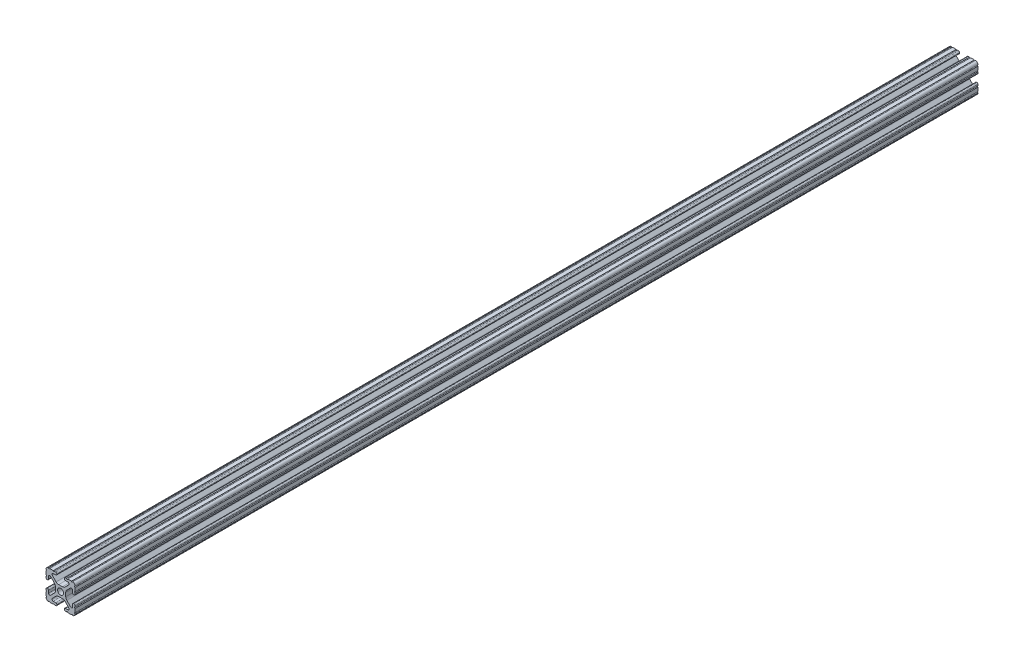
SolidWorks part; units mm, degrees
ref_plane "Front Plane" through (0, 0, 0) normal (0, 0, 1) x (1, 0, 0)
ref_plane "Top Plane" through (0, 0, 0) normal (0, 1, 0) x (1, 0, 0)
ref_plane "Right Plane" through (0, 0, 0) normal (1, 0, 0) x (0, 0, -1)
sketch "Sketch1" plane through (0, 0, 0) normal (0, 0, 1) x (1, 0, 0)
  line L88 (-7.1797, -8.6452) -> (-3.9523, -5.4237)
  line L89 (-1.7093, -4.4958) -> (1.7093, -4.4958)
  line L90 (3.9523, -5.4237) -> (7.1797, -8.6452)
  line L91 (6.4164, -10.4902) -> (4.2875, -10.4902)
  line L92 (3.2385, -11.5392) -> (3.2385, -11.651)
  line L93 (4.2875, -12.7) -> (5.3171, -12.7)
  line L94 (6.3331, -12.7) -> (9.5504, -12.7)
  line L95 (12.7, -9.5504) -> (12.7, -6.3331)
  line L96 (12.7, -5.3171) -> (12.7, -4.2875)
  line L97 (11.651, -3.2385) -> (11.5392, -3.2385)
  line L98 (10.4902, -4.2875) -> (10.4902, -6.4021)
  line L99 (8.7371, -7.1294) -> (5.441, -3.8408)
  line L100 (4.5085, -1.5932) -> (4.5085, 1.5932)
  line L101 (5.441, 3.8408) -> (8.7371, 7.1294)
  line L102 (10.4902, 6.4021) -> (10.4902, 4.2875)
  line L103 (11.5392, 3.2385) -> (11.651, 3.2385)
  line L104 (12.7, 4.2875) -> (12.7, 5.3171)
  line L105 (12.7, 6.3331) -> (12.7, 9.5504)
  line L106 (9.5504, 12.7) -> (6.3331, 12.7)
  line L107 (5.3171, 12.7) -> (4.2875, 12.7)
  line L108 (3.2385, 11.651) -> (3.2385, 11.5392)
  line L109 (4.2875, 10.4902) -> (6.4768, 10.4902)
  line L110 (7.207, 8.7244) -> (3.8983, 5.4232)
  line L111 (1.6558, 4.4958) -> (-1.6558, 4.4958)
  line L112 (-3.8983, 5.4232) -> (-7.207, 8.7244)
  line L113 (-6.4768, 10.4902) -> (-4.2875, 10.4902)
  line L114 (-3.2385, 11.5392) -> (-3.2385, 11.651)
  line L115 (-4.2875, 12.7) -> (-5.3171, 12.7)
  line L116 (-6.3331, 12.7) -> (-9.5504, 12.7)
  line L117 (-12.7, 9.5504) -> (-12.7, 6.3331)
  line L118 (-12.7, 5.3171) -> (-12.7, 4.2875)
  line L119 (-11.651, 3.2385) -> (-11.5392, 3.2385)
  line L120 (-10.4902, 4.2875) -> (-10.4902, 6.4021)
  line L121 (-8.7371, 7.1294) -> (-5.441, 3.8408)
  line L122 (-4.5085, 1.5932) -> (-4.5085, -1.5932)
  line L123 (-5.441, -3.8408) -> (-8.7371, -7.1294)
  line L124 (-10.4902, -6.4021) -> (-10.4902, -4.2875)
  line L125 (-11.5392, -3.2385) -> (-11.651, -3.2385)
  line L126 (-12.7, -4.2875) -> (-12.7, -5.3171)
  line L127 (-12.7, -6.3331) -> (-12.7, -9.5504)
  line L128 (-9.5504, -12.7) -> (-6.3331, -12.7)
  line L129 (-5.3171, -12.7) -> (-4.2875, -12.7)
  line L130 (-3.2385, -11.651) -> (-3.2385, -11.5392)
  line L131 (-4.2875, -10.4902) -> (-6.4164, -10.4902)
  circle A1 centre (0, 0) radius 2.6035
  arc A104 (-7.1797, -8.6452) -> (-6.4164, -10.4902) centre (-6.4164, -9.4098) ccw
  arc A105 (-1.7093, -4.4958) -> (-3.9523, -5.4237) centre (-1.7093, -7.6708) ccw
  arc A106 (3.9523, -5.4237) -> (1.7093, -4.4958) centre (1.7093, -7.6708) ccw
  arc A107 (6.4164, -10.4902) -> (7.1797, -8.6452) centre (6.4164, -9.4098) ccw
  arc A108 (4.2875, -10.4902) -> (3.2385, -11.5392) centre (4.2875, -11.5392) ccw
  arc A109 (3.2385, -11.651) -> (4.2875, -12.7) centre (4.2875, -11.651) ccw
  arc A110 (6.3331, -12.7) -> (5.3171, -12.7) centre (5.8251, -12.7) ccw
  arc A111 (10.5664, -12.6998) -> (9.5504, -12.7) centre (10.0584, -12.7) ccw
  arc A112 (10.5664, -12.6998) -> (12.6998, -10.5664) centre (10.5918, -10.5918) ccw
  arc A113 (12.7, -9.5504) -> (12.6998, -10.5664) centre (12.7, -10.0584) ccw
  arc A114 (12.7, -5.3171) -> (12.7, -6.3331) centre (12.7, -5.8251) ccw
  arc A115 (12.7, -4.2875) -> (11.651, -3.2385) centre (11.651, -4.2875) ccw
  arc A116 (11.5392, -3.2385) -> (10.4902, -4.2875) centre (11.5392, -4.2875) ccw
  arc A117 (8.7371, -7.1294) -> (10.4902, -6.4021) centre (9.4628, -6.4021) ccw
  arc A118 (4.5085, -1.5932) -> (5.441, -3.8408) centre (7.6835, -1.5932) ccw
  arc A119 (5.441, 3.8408) -> (4.5085, 1.5932) centre (7.6835, 1.5932) ccw
  arc A120 (10.4902, 6.4021) -> (8.7371, 7.1294) centre (9.4628, 6.4021) ccw
  arc A121 (10.4902, 4.2875) -> (11.5392, 3.2385) centre (11.5392, 4.2875) ccw
  arc A122 (11.651, 3.2385) -> (12.7, 4.2875) centre (11.651, 4.2875) ccw
  arc A123 (12.7, 6.3331) -> (12.7, 5.3171) centre (12.7, 5.8251) ccw
  arc A124 (12.6998, 10.5664) -> (12.7, 9.5504) centre (12.7, 10.0584) ccw
  arc A125 (12.6998, 10.5664) -> (10.5664, 12.6998) centre (10.5918, 10.5918) ccw
  arc A126 (9.5504, 12.7) -> (10.5664, 12.6998) centre (10.0584, 12.7) ccw
  arc A127 (5.3171, 12.7) -> (6.3331, 12.7) centre (5.8251, 12.7) ccw
  arc A128 (4.2875, 12.7) -> (3.2385, 11.651) centre (4.2875, 11.651) ccw
  arc A129 (3.2385, 11.5392) -> (4.2875, 10.4902) centre (4.2875, 11.5392) ccw
  arc A130 (7.207, 8.7244) -> (6.4768, 10.4902) centre (6.4768, 9.4563) ccw
  arc A131 (1.6558, 4.4958) -> (3.8983, 5.4232) centre (1.6558, 7.6708) ccw
  arc A132 (-3.8983, 5.4232) -> (-1.6558, 4.4958) centre (-1.6558, 7.6708) ccw
  arc A133 (-6.4768, 10.4902) -> (-7.207, 8.7244) centre (-6.4768, 9.4563) ccw
  arc A134 (-4.2875, 10.4902) -> (-3.2385, 11.5392) centre (-4.2875, 11.5392) ccw
  arc A135 (-3.2385, 11.651) -> (-4.2875, 12.7) centre (-4.2875, 11.651) ccw
  arc A136 (-6.3331, 12.7) -> (-5.3171, 12.7) centre (-5.8251, 12.7) ccw
  arc A137 (-10.5664, 12.6998) -> (-9.5504, 12.7) centre (-10.0584, 12.7) ccw
  arc A138 (-10.5664, 12.6998) -> (-12.6998, 10.5664) centre (-10.5918, 10.5918) ccw
  arc A139 (-12.7, 9.5504) -> (-12.6998, 10.5664) centre (-12.7, 10.0584) ccw
  arc A140 (-12.7, 5.3171) -> (-12.7, 6.3331) centre (-12.7, 5.8251) ccw
  arc A141 (-12.7, 4.2875) -> (-11.651, 3.2385) centre (-11.651, 4.2875) ccw
  arc A142 (-11.5392, 3.2385) -> (-10.4902, 4.2875) centre (-11.5392, 4.2875) ccw
  arc A143 (-8.7371, 7.1294) -> (-10.4902, 6.4021) centre (-9.4628, 6.4021) ccw
  arc A144 (-4.5085, 1.5932) -> (-5.441, 3.8408) centre (-7.6835, 1.5932) ccw
  arc A145 (-5.441, -3.8408) -> (-4.5085, -1.5932) centre (-7.6835, -1.5932) ccw
  arc A146 (-10.4902, -6.4021) -> (-8.7371, -7.1294) centre (-9.4628, -6.4021) ccw
  arc A147 (-10.4902, -4.2875) -> (-11.5392, -3.2385) centre (-11.5392, -4.2875) ccw
  arc A148 (-11.651, -3.2385) -> (-12.7, -4.2875) centre (-11.651, -4.2875) ccw
  arc A149 (-12.7, -6.3331) -> (-12.7, -5.3171) centre (-12.7, -5.8251) ccw
  arc A150 (-12.6998, -10.5664) -> (-12.7, -9.5504) centre (-12.7, -10.0584) ccw
  arc A151 (-12.6998, -10.5664) -> (-10.5664, -12.6998) centre (-10.5918, -10.5918) ccw
  arc A152 (-9.5504, -12.7) -> (-10.5664, -12.6998) centre (-10.0584, -12.7) ccw
  arc A153 (-5.3171, -12.7) -> (-6.3331, -12.7) centre (-5.8251, -12.7) ccw
  arc A154 (-4.2875, -12.7) -> (-3.2385, -11.651) centre (-4.2875, -11.651) ccw
  arc A155 (-3.2385, -11.5392) -> (-4.2875, -10.4902) centre (-4.2875, -11.5392) ccw
extrude "Boss-Extrude1" add sketch "Sketch1" along normal mid plane 787.4
sketch "Sketch2" plane through (4.5085, 0, 0) normal (1, 0, 0) x (0, 0, -1)
  line L0 (0, 0) -> (-393.7, 0) construction
  line L1 (-393.7, -1.5932) -> (-393.7, 1.5932) construction
  line L2 (0, 0) -> (0, 58.4486) construction
  circle A0 centre (-279.4, 0) radius 3.175
  circle A1 centre (279.4, 0) radius 3.175
  circle A2 centre (-12.7, 0) radius 3.175
  circle A3 centre (12.7, 0) radius 3.175
  point P15 (0, 0)
  dimension "D1" = 6.35
  dimension "D2" = 114.3
  dimension "D3" = 6.35
  dimension "D4" = 266.7
extrude "Cut-Extrude1" cut sketch "Sketch2" against normal through all both and the other way through all
